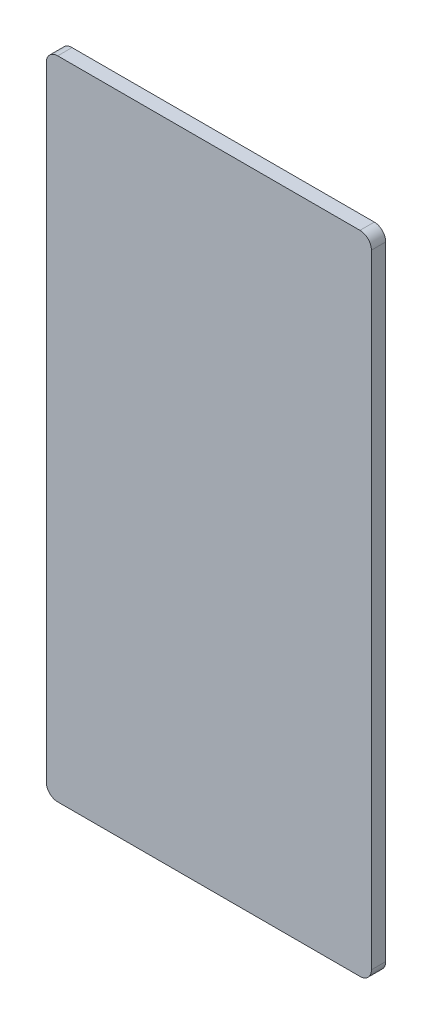
SolidWorks part; units mm, degrees
material "ABS"
ref_plane "X-Y Datum" through (0, 0, 0) normal (0, 0, 1) x (1, 0, 0)
ref_plane "X-Z Datum" through (0, 0, 0) normal (0, 1, 0) x (1, 0, 0)
ref_plane "Y-Z Datum" through (0, 0, 0) normal (1, 0, 0) x (0, 0, -1)
sketch "Sketch1" plane through (0, 0, 0) normal (0, 0, 1) x (1, 0, 0)
  line L1 (0, 0) -> (72.1385, 0)
  line L2 (0, 0) -> (0, 143.3432)
  line L3 (0, 143.3432) -> (72.1385, 143.3432)
  line L4 (72.1385, 0) -> (72.1385, 143.3432)
extrude "Boss-Extrude1" add sketch "Sketch1" along normal blind 3.175
fillet "Fillet1" radius 2.54 4 edges at (0, 143.3432, 1.5875) (0, 0, 1.5875) (72.1385, 0, 1.5875) (72.1385, 143.3432, 1.5875)
